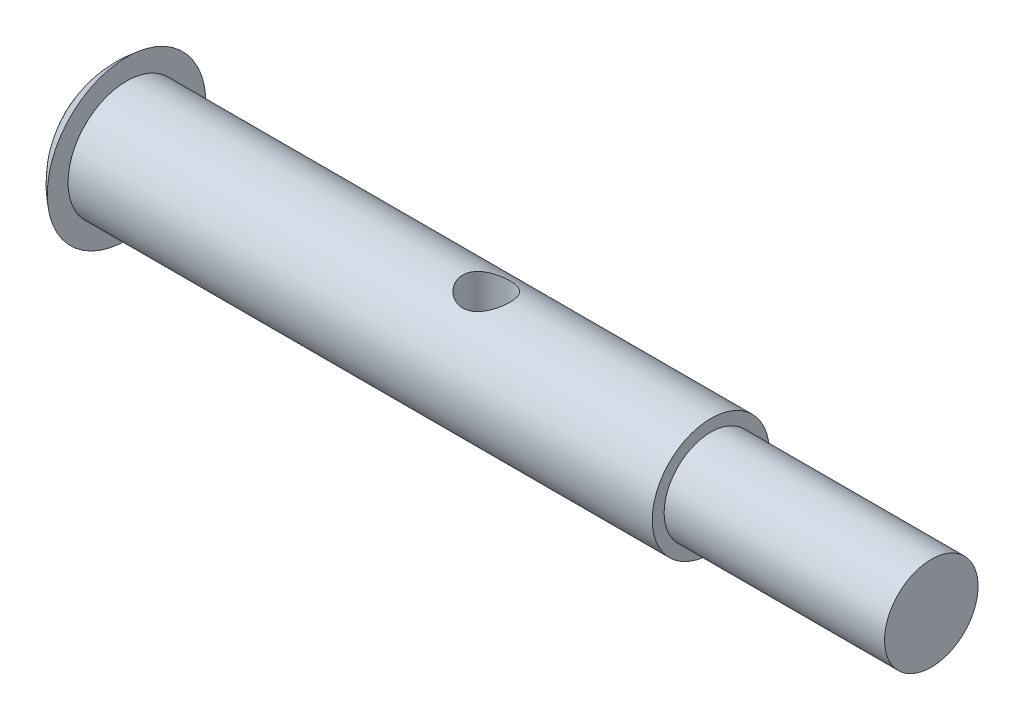
SolidWorks part; units mm, degrees
material "Plain Carbon Steel"
ref_plane "Front Plane" through (0, 0, 0) normal (0, 0, 1) x (1, 0, 0)
ref_plane "Top Plane" through (0, 0, 0) normal (0, 1, 0) x (1, 0, 0)
ref_plane "Right Plane" through (0, 0, 0) normal (1, 0, 0) x (0, 0, -1)
sketch "Sketch1" plane through (0, 0, 0) normal (0, 0, 1) x (1, 0, 0)
  line L0 (0, 0) -> (36.9482, 0) construction
  line L1 (0, 3.3274) -> (0, 2.4574)
  line L2 (0, 2.4574) -> (24.511, 2.4574)
  line L3 (24.511, 2.4574) -> (24.511, 1.9622)
  line L4 (24.511, 1.9622) -> (33.7566, 1.9621)
  line L5 (33.7566, 1.9621) -> (33.7566, 0)
  line L6 (-1.651, 0) -> (33.7566, 0)
  arc A0 (0, 3.3274) -> (-1.651, 0) centre (2.5275, 0) ccw
  dimension "D1" = 35.4076
  dimension "D2" = 33.7566
  dimension "D3" = 9.2456
  dimension "D4" = 4.9149
  dimension "D5" = 3.9243
  dimension "D6" = 6.6548
revolve "Revolve1" add sketch "Sketch1" angle 360 about L0
sketch "Sketch4" plane through (0, 0, 0) normal (0, 1, 0) x (1, 0, 0)
  line L0 (33.7566, -1.9621) -> (33.7566, 1.9621) construction
  circle A0 centre (15.0876, 0) radius 0.9906
  dimension "D1" = 1.9812
  dimension "D2" = 18.669
extrude "Cut-Extrude1" cut sketch "Sketch4" against normal through all both and the other way through all
